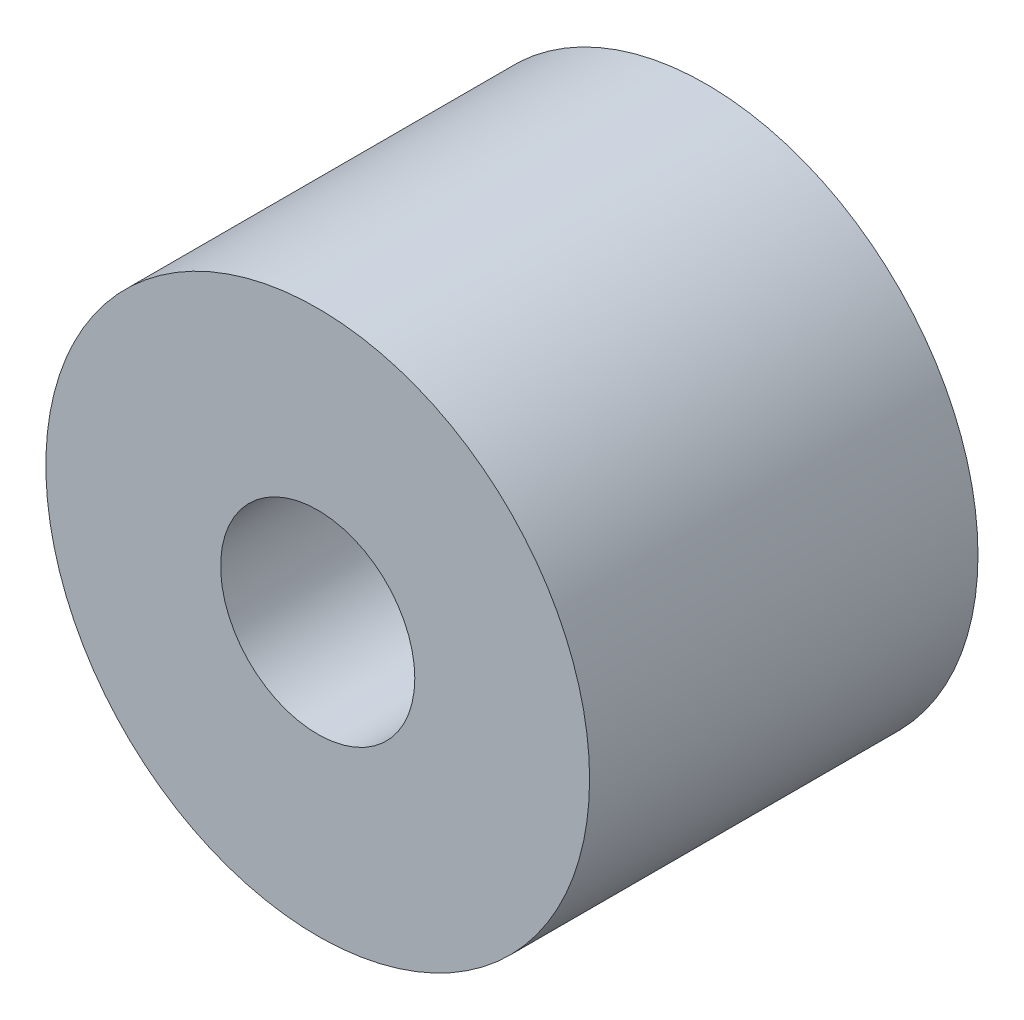
SolidWorks part; units mm, degrees
ref_plane "Front Plane" through (0, 0, 0) normal (0, 0, 1) x (1, 0, 0)
ref_plane "Top Plane" through (0, 0, 0) normal (0, 1, 0) x (1, 0, 0)
ref_plane "Right Plane" through (0, 0, 0) normal (1, 0, 0) x (0, 0, -1)
sketch "Sketch1" plane through (0, 0, 0) normal (0, 0, 1) x (1, 0, 0)
  circle A0 centre (0, 0) radius 3.5
  circle A1 centre (0, 0) radius 1.25
  dimension "D1" = 7
  dimension "D2" = 2.5
extrude "Boss-Extrude1" add sketch "Sketch1" along normal blind 5
